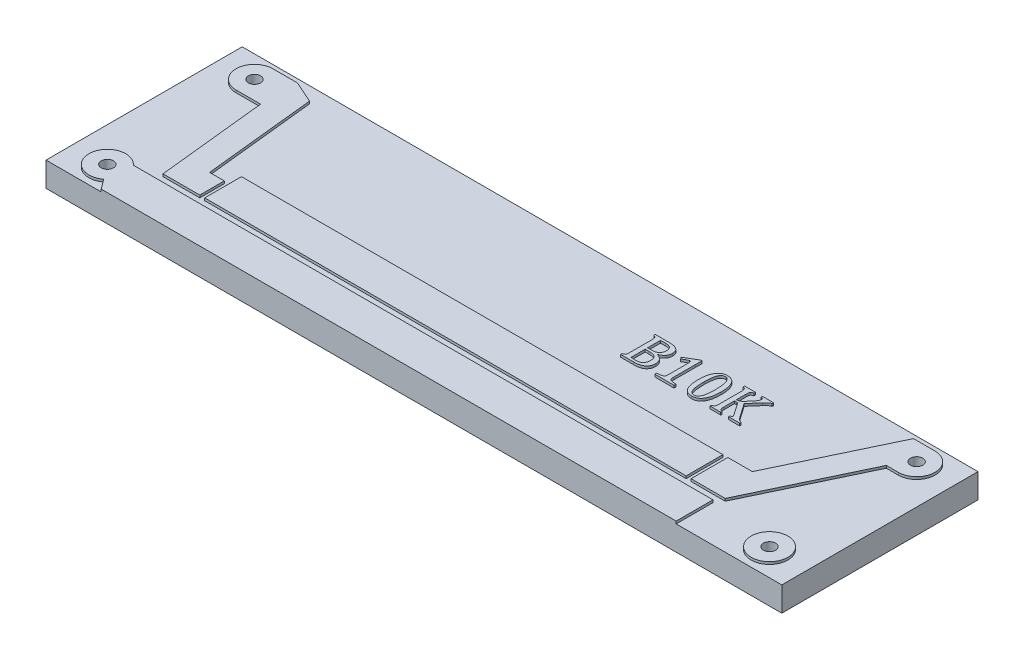
SolidWorks part; units mm, degrees
ref_plane "前视基准面" through (0, 0, 0) normal (0, 0, 1) x (1, 0, 0)
ref_plane "上视基准面" through (0, 0, 0) normal (0, 1, 0) x (1, 0, 0)
ref_plane "右视基准面" through (0, 0, 0) normal (1, 0, 0) x (0, 0, -1)
sketch "草图1" plane through (0, 0, 0) normal (0, 1, 0) x (1, 0, 0)
  line L1 (-15, 4) -> (15, 4)
  line L2 (-15, 4) -> (-15, -4)
  line L3 (-15, -4) -> (15, -4)
  line L4 (15, 4) -> (15, -4)
  line L5 (-15, 4) -> (15, -4) construction
  line L6 (-15, -4) -> (15, 4) construction
  point P0 (0, 0)
  dimension "D1" = 30
  dimension "D2" = 8
extrude "凸台-拉伸1" add sketch "草图1" along normal blind 1
sketch "草图2" plane through (0, 1, 0) normal (0, 1, 0) x (1, 0, 0)
  line L0 (15, 4) -> (-15, 4) construction
  line L1 (-15, 4) -> (-15, -4) construction
  line L2 (-15, 0) -> (15, 0) construction
  line L3 (15, -4) -> (15, 4) construction
  line L4 (0, 4) -> (0, -4) construction
  line L5 (-15, -4) -> (15, -4) construction
  circle A0 centre (-13.5, 3) radius 0.25
  circle A1 centre (13.5, 3) radius 0.25
  circle A2 centre (13.5, -3) radius 0.25
  circle A3 centre (-13.5, -3) radius 0.25
  dimension "D1" = 1
  dimension "D2" = 1.5
extrude "切除-拉伸1" cut sketch "草图2" against normal mid plane 3
sketch "草图3" plane through (0, 1, 0) normal (0, 1, 0) x (1, 0, 0)
  line L0 (10.6933, -2.5) -> (-12.941, -2.5)
  line L1 (10.6933, -2.5) -> (10.6933, -4)
  line L2 (-15, -4) -> (15, -4) construction
  line L3 (10.6933, -4) -> (-12.75, -4)
  line L4 (-12.75, -4) -> (-13.05, -3.6)
  line L5 (9.5, -0.7) -> (10.5, -0.7)
  line L6 (10.5, -0.7) -> (12.619, 3.75)
  line L7 (12.619, 3.75) -> (13.5, 3.75)
  line L8 (9.5, -0.7) -> (9.5, -2.2)
  line L9 (9.5, -2.2) -> (10.8933, -2.2)
  line L10 (10.8933, -2.2) -> (13.0124, 2.25)
  line L11 (13.0124, 2.25) -> (13.5, 2.25)
  line L12 (-13.5, 3.75) -> (-12.5, 3.75)
  line L13 (-12.5, 3.75) -> (-11.6111, 3.3547)
  line L14 (-11.6111, 3.3547) -> (-11.1303, -1.2)
  line L15 (-11.1303, -1.2) -> (-10.5303, -1.2)
  line L16 (-10.5303, -1.2) -> (-10.5303, -2.2)
  line L17 (-10.5303, -2.2) -> (-12.0303, -2.2)
  line L18 (-12.5, 2.25) -> (-12.0303, -2.2)
  line L19 (-12.5, 2.25) -> (-13.5, 2.25)
  line L21 (-10.3303, -0.7) -> (9.3, -0.7)
  line L22 (-10.3303, -0.7) -> (-10.3303, -2.2)
  line L23 (-10.3303, -2.2) -> (9.3, -2.2)
  line L24 (9.3, -0.7) -> (9.3, -2.2)
  arc A0 (-12.941, -2.5) -> (-13.05, -3.6) centre (-13.5, -3) ccw
  arc A1 (-13.5, 3.75) -> (-13.5, 2.25) centre (-13.5, 3) ccw
  circle A2 centre (13.5, -3) radius 0.75
  arc A3 (13.5, 2.25) -> (13.5, 3.75) centre (13.5, 3) ccw
  dimension "D1" = 1.5
  dimension "D8" = 1.5
  dimension "D21" = 1.5
  dimension "D9" = 1.5
  dimension "D2" = 1.5
  dimension "D3" = 1
  dimension "D4" = 0.6
  dimension "D5" = 1.5
  dimension "D6" = 1
  dimension "D10" = 1
  dimension "D11" = 1
  dimension "D14" = 1
  dimension "D15" = 1.5
  dimension "D16" = 0.2
  dimension "D17" = 0.2
  dimension "D18" = 19.6303
  dimension "D19" = 0.2
  dimension "D20" = 0.3
extrude "凸台-拉伸2" add sketch "草图3" along normal blind 0.1
sketch "草图4" plane through (0, 1.1, 0) normal (0, 1, 0) x (1, 0, 0)
  circle A1 centre (13.5, 3) radius 0.25
  circle A2 centre (13.5, 3) radius 0.25
  circle A3 centre (-13.5, 3) radius 0.25
  circle A4 centre (-13.5, 3) radius 0.25
  circle A5 centre (-13.5, -3) radius 0.25
  circle A6 centre (-13.5, -3) radius 0.25
  circle A7 centre (13.5, -3) radius 0.25
  circle A8 centre (13.5, -3) radius 0.25
  dimension "D1" = 0
  dimension "D2" = 0
  dimension "D3" = 0
  dimension "D4" = 0
extrude "切除-拉伸2" cut sketch "草图4" against normal blind 10
sketch "草图5" plane through (0, 1, 0) normal (0, 1, 0) x (1, 0, 0)
  text T0 "B10K" font "Cambria" height in points 4
extrude "凸台-拉伸3" add sketch "草图5" along normal blind 0.1
